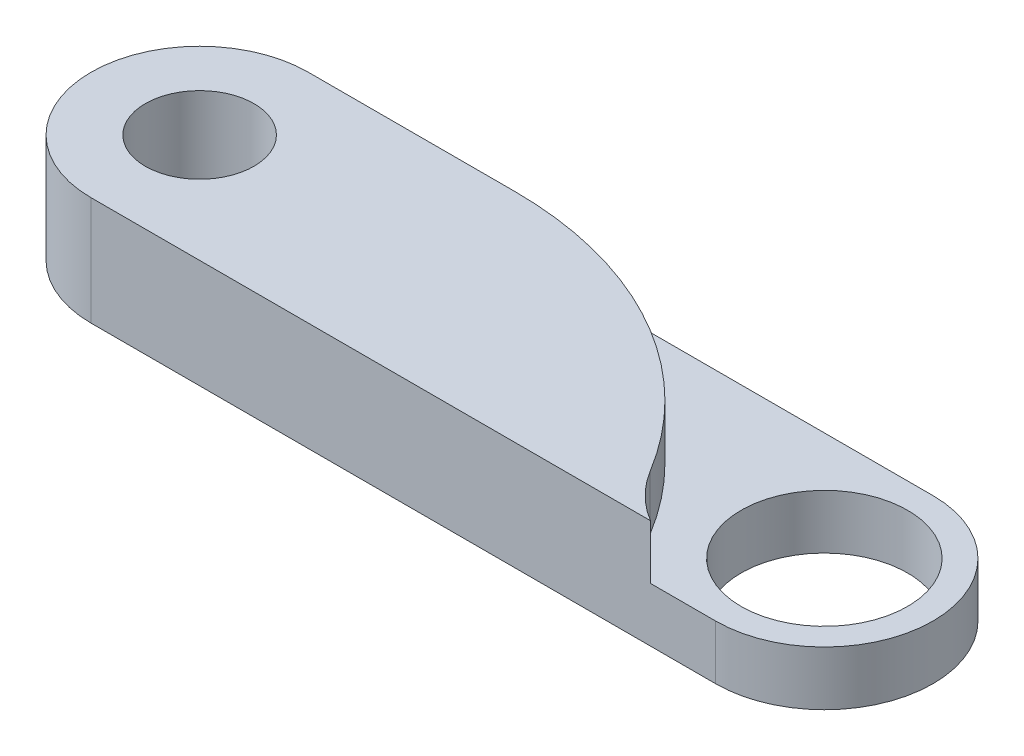
SolidWorks part; units mm, degrees
material "ABS"
ref_plane "正面" through (0, 0, 0) normal (0, 0, 1) x (1, 0, 0)
ref_plane "平面" through (0, 0, 0) normal (0, 1, 0) x (1, 0, 0)
ref_plane "右側面" through (0, 0, 0) normal (1, 0, 0) x (0, 0, -1)
sketch "ｽｹｯﾁ1" plane through (0, 0, 0) normal (0, 1, 0) x (1, 0, 0)
  line L0 (-17.25, 0) -> (17.25, 0) construction
  line L1 (-17.25, 6) -> (17.25, 6)
  line L2 (-17.25, -6) -> (17.25, -6)
  arc A0 (-17.25, 6) -> (-17.25, -6) centre (-17.25, 0) ccw
  arc A1 (17.25, -6) -> (17.25, 6) centre (17.25, 0) ccw
  circle A2 centre (-17.25, 0) radius 3
  circle A3 centre (17.25, 0) radius 4.6
  point P2 (0, 0)
  dimension "D2" = 6
  dimension "D3" = 6
  dimension "D4" = 9.2
  dimension "D1" = 34.5
extrude "ﾎﾞｽ - 押し出し1" add sketch "ｽｹｯﾁ1" along normal blind 6
sketch "ｽｹｯﾁ3" plane through (0, 6, 0) normal (0, 1, 0) x (1, 0, 0)
  circle A0 centre (17.25, 0) radius 7
  circle A1 centre (17.25, 0) radius 4.6 construction
  dimension "D1" = 14
extrude "ｶｯﾄ - 押し出し1" cut sketch "ｽｹｯﾁ3" against normal blind 3
fillet "ﾌｨﾚｯﾄ1" radius 20 1 edges at (13.6444, 4.5, -6)
